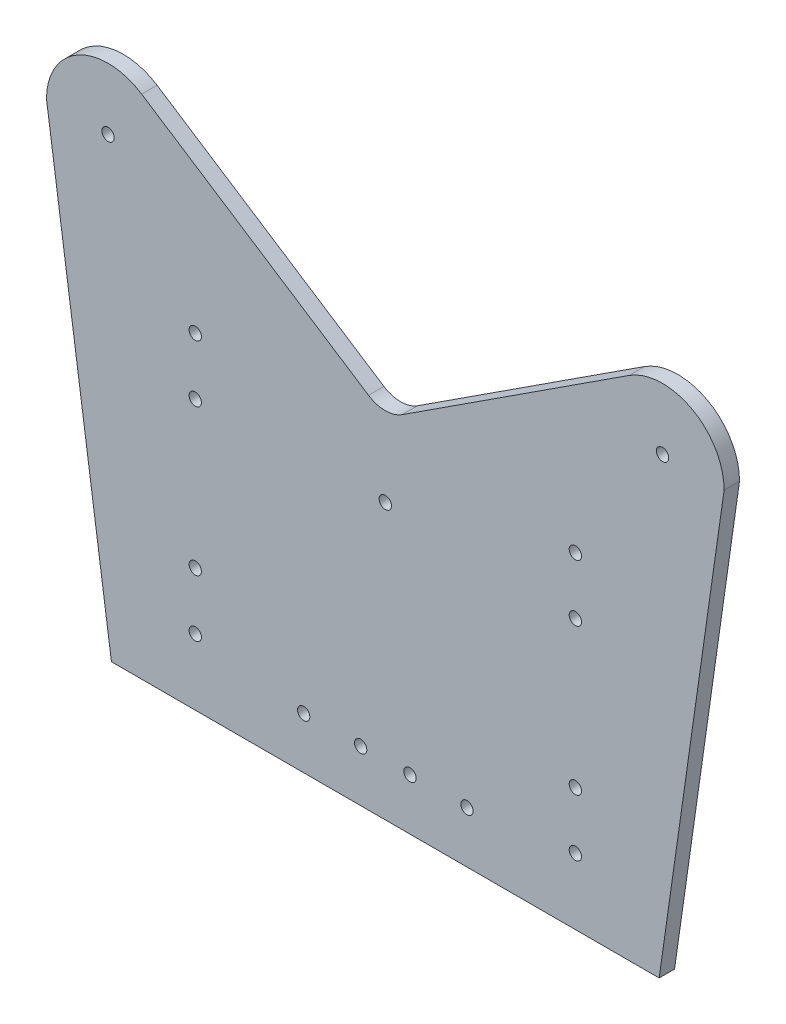
SolidWorks part; units mm, degrees
ref_plane "前视基准面" through (0, 0, 0) normal (0, 0, 1) x (1, 0, 0)
ref_plane "上视基准面" through (0, 0, 0) normal (0, 1, 0) x (1, 0, 0)
ref_plane "右视基准面" through (0, 0, 0) normal (1, 0, 0) x (0, 0, -1)
sketch "草图1" plane through (0, 0, 0) normal (0, 0, 1) x (1, 0, 0)
  line L0 (-25.0786, 81.7587) -> (-38.9236, 5.8977)
  line L1 (-34.0049, 0) -> (34.0049, 0)
  line L2 (0, -55) -> (0, 55) construction
  line L3 (25.6841, 78.4413) -> (38.9236, 5.8977)
  line L4 (0, 89.27) -> (90, 147.74) construction
  line L5 (0, 89.27) -> (-90, 147.74) construction
  line L6 (27.8788, 83.5319) -> (100.8958, 130.9686)
  line L7 (79.1042, 164.5114) -> (5.4479, 116.6594)
  line L8 (-79.1042, 164.5114) -> (-5.4479, 116.6594)
  line L9 (-27.8788, 83.5319) -> (-100.8958, 130.9686)
  line L10 (-110, 147.74) -> (-88.9121, 0)
  line L11 (-88.9121, 0) -> (88.9121, 0)
  line L12 (110, 147.74) -> (88.9121, 0)
  circle A0 centre (0, 89.27) radius 2
  arc A2 (38.9236, 5.8977) -> (34.0049, 0) centre (34.0049, 5) cw
  arc A3 (-34.0049, 0) -> (-38.9236, 5.8977) centre (-34.0049, 5) cw
  circle A4 centre (90, 147.74) radius 2
  arc A6 (79.1042, 164.5114) -> (100.8958, 130.9686) centre (90, 147.74) cw
  arc A8 (27.8788, 83.5319) -> (25.6841, 78.4413) centre (30.6028, 79.339) ccw
  circle A11 centre (-26.5, 16.7) radius 2
  circle A12 centre (-8, 16.7) radius 2
  circle A13 centre (8, 16.7) radius 2
  circle A14 centre (26.5, 16.7) radius 2
  arc A15 (-27.8788, 83.5319) -> (-25.6841, 78.4413) centre (-30.6028, 79.339) cw
  arc A16 (-79.1042, 164.5114) -> (-100.8958, 130.9686) centre (-90, 147.74) ccw
  circle A17 centre (-90, 147.74) radius 2
  arc A18 (-5.4479, 116.6594) -> (5.4479, 116.6594) centre (0, 125.0451) ccw
  circle A19 centre (-61.7, 105.9731) radius 2
  circle A20 centre (-61.7, 87.4731) radius 2
  circle A21 centre (61.7, 87.4731) radius 2
  circle A22 centre (61.7, 105.9731) radius 2
  circle A23 centre (61.7, 39.9731) radius 2
  circle A24 centre (-61.7, 39.9731) radius 2
  circle A25 centre (-61.7, 21.4731) radius 2
  circle A26 centre (61.7, 21.4731) radius 2
  point P9 (0, 0)
  point P11 (0, 219.1718)
  point P14 (40, 0)
  point P17 (-40, 0)
  point P30 (25.0861, 81.7175)
  point P45 (-25.0861, 81.7175)
  point P55 (0, 0)
  point P64 (0, 0)
  point P65 (0, 0)
  point P66 (0, 0)
  point P67 (0, 0)
  point P68 (-61.7, 64.037)
  point P69 (0, 0)
  point P70 (0, 0)
  point P71 (0, 0)
  point P72 (-61.7, 64.037)
  point P73 (0, 0)
  point P74 (0, 0)
  point P75 (0, 0)
  point P76 (-61.7, 64.037)
  point P77 (-61.7, 64.037)
  point P78 (0, 0)
  point P79 (0, 0)
  point P80 (0, 0)
  point P81 (-59.9782, 38.4456)
  point P82 (-60.0505, 39.9938)
  point P83 (0, 0)
  point P84 (61.7, 39.9731)
  point P85 (61.7, 21.4731)
  point P86 (-88.9121, 0)
  point P87 (-92.0794, 125.0451)
  point P88 (-111.5131, 137.8662)
  point P89 (-96.5025, 128.1144)
  point P90 (0, 0)
  point P91 (-110, 147.74)
  dimension "D2" = 4
  dimension "D4" = 58.47
  dimension "D5" = 5
  dimension "D6" = 90
  dimension "D9" = 5
  dimension "D10" = 18.5
  dimension "D13" = 10
  dimension "D17" = 4
  dimension "D18" = 4
  dimension "D19" = 4
  dimension "D1" = 40
  dimension "D3" = 89.27
  dimension "D7" = 20
  dimension "D8" = 20
  dimension "D11" = 16.7
  dimension "D12" = 8
  dimension "D14" = 0
  dimension "D15" = 87.8354
  dimension "D16" = 72.5436
  dimension "D20" = 18.5
  dimension "D21" = 61.7
  dimension "D22" = 18.5
  dimension "D23" = 66
extrude "凸台-拉伸1" add sketch "草图1" along normal blind 5
